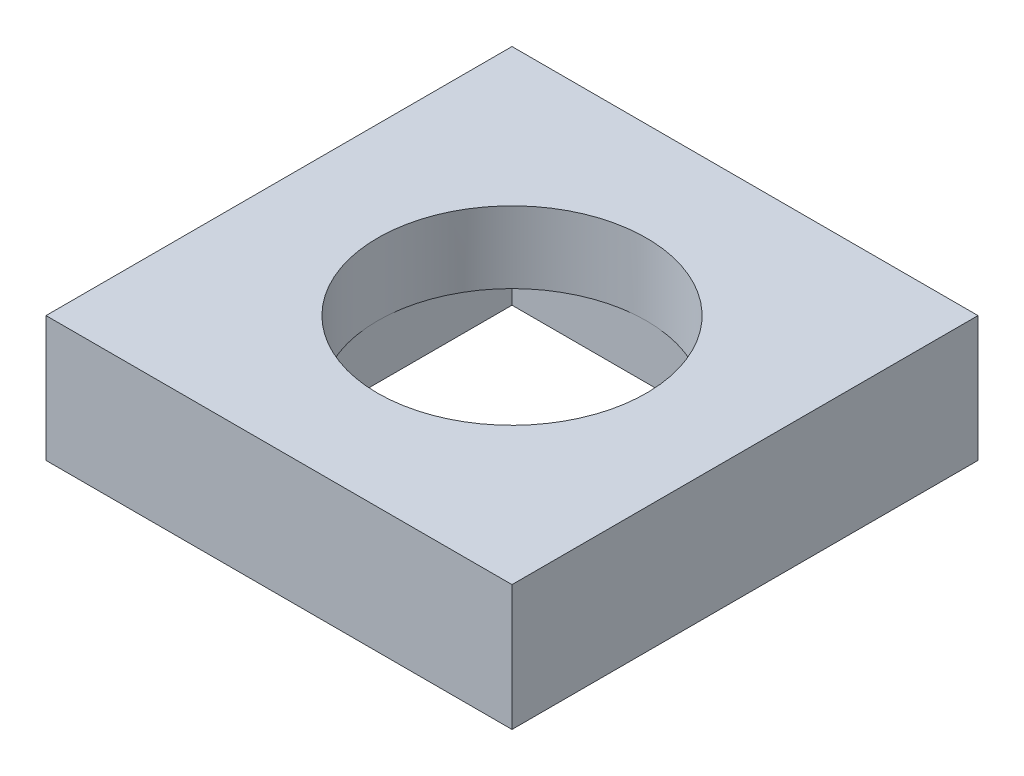
SolidWorks part; units mm, degrees
ref_plane "Front Plane" through (0, 0, 0) normal (0, 0, 1) x (1, 0, 0)
ref_plane "Top Plane" through (0, 0, 0) normal (0, 1, 0) x (1, 0, 0)
ref_plane "Right Plane" through (0, 0, 0) normal (1, 0, 0) x (0, 0, -1)
sketch "Sketch1" plane through (0, 0, 0) normal (0, 1, 0) x (1, 0, 0)
  line L1 (-1.6118, 0.5904) -> (0.9882, 0.5904)
  line L2 (-1.6118, 0.5904) -> (-1.6118, -2.0096)
  line L3 (-1.6118, -2.0096) -> (0.9882, -2.0096)
  line L4 (0.9882, 0.5904) -> (0.9882, -2.0096)
  circle A0 centre (-0.3118, -0.7096) radius 0.75
  dimension "D3" = 1.3
  dimension "D1" = 2.6
  dimension "D2" = 2.6
  dimension "D4" = 1.3
extrude "Boss-Extrude1" add sketch "Sketch1" along normal blind 0.7
sketch "Sketch2" plane through (0, 0, 0) normal (0, -1, 0) x (1, 0, 0)
  line L1 (-1.0618, 1.4596) -> (0.4382, 1.4596)
  line L2 (-1.0618, 1.4596) -> (-1.0618, -0.0404)
  line L3 (-1.0618, -0.0404) -> (0.4382, -0.0404)
  line L4 (0.4382, 1.4596) -> (0.4382, -0.0404)
  circle A0 centre (-0.3118, 0.7096) radius 0.75 construction
  dimension "D1" = 1.5
  dimension "D2" = 1.5
  dimension "D3" = 0.75
  dimension "D4" = 0.75
extrude "Cut-Extrude1" cut sketch "Sketch2" against normal blind 0.3
